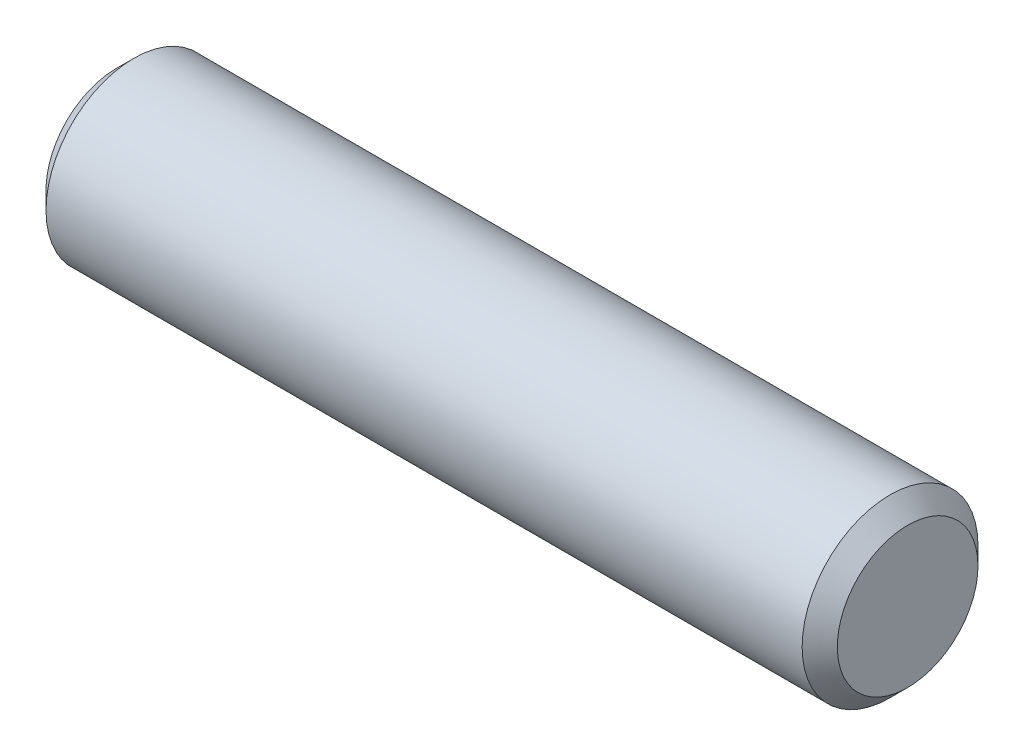
SolidWorks part; units mm, degrees
ref_plane "Front" through (0, 0, 0) normal (0, 0, 1) x (1, 0, 0)
ref_plane "Top" through (0, 0, 0) normal (0, 1, 0) x (1, 0, 0)
ref_plane "Right" through (0, 0, 0) normal (1, 0, 0) x (0, 0, -1)
sketch "Sketch1" plane through (0, 0, 0) normal (0, 0, 1) x (1, 0, 0)
  line L0 (-7.1438, 0) -> (7.1438, 0) construction
  line L1 (7.1438, 1.5875) -> (7.1438, -1.5875) construction
  line L2 (-7.1438, 1.5875) -> (-7.1438, -1.5875) construction
  dimension "Length" = 14.2875
  dimension "Diameter" = 3.175
sketch "Sketch2" plane through (0, 0, 0) normal (1, 0, 0) x (0, 0, -1)
  circle A0 centre (0, 0) radius 1.5875
extrude "Extrude1" add sketch "Sketch2" against normal up to vertex (7.1437 mm away) and the other way up to vertex (7.1437 mm away) up to point (-7.1438, 1.5875, 0) other way up to point (7.1438, 1.5875, 0)
chamfer "Chamfer1" distance 0.3175 angle 45 2 edges at (7.1438, 0, -1.5875) (-7.1438, 0, -1.5875)
equation "\"D1@Chamfer1\" = \"Diameter@Sketch1\"*.1"
